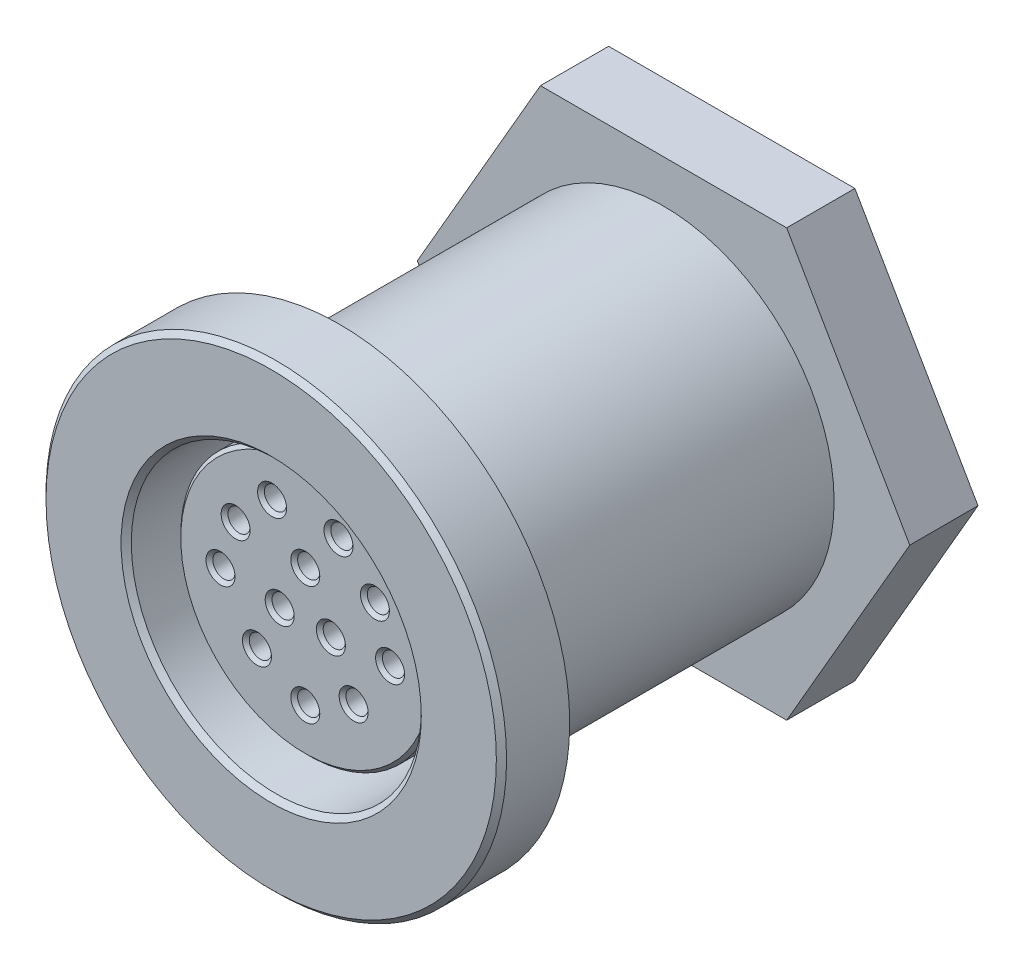
SolidWorks part; units mm, degrees
material "1060 Alloy"
ref_plane "Front Plane" through (0, 0, 0) normal (0, 0, 1) x (1, 0, 0)
ref_plane "Top Plane" through (0, 0, 0) normal (0, 1, 0) x (1, 0, 0)
ref_plane "Right Plane" through (0, 0, 0) normal (1, 0, 0) x (0, 0, -1)
sketch "Sketch1" plane through (0, 0, 0) normal (0, 0, 1) x (1, 0, 0)
  circle A0 centre (0, 0) radius 13.5
extrude "Extrude1" add sketch "Sketch1" along normal blind 4
sketch "Sketch3" plane through (0, 0, 0) normal (0, 0, -1) x (-1, 0, 0)
  circle A0 centre (0, 0) radius 10
extrude "Extrude3" add sketch "Sketch3" along normal blind 25
sketch "Sketch7" plane through (0, 0, 4) normal (0, 0, 1) x (1, 0, 0)
  circle A0 centre (0, 0) radius 8.5
extrude "Cut-Extrude5" cut sketch "Sketch7" against normal blind 16
sketch "Sketch4" plane through (0, 0, -12) normal (0, 0, 1) x (1, 0, 0)
  circle A0 centre (0, 0) radius 7.5
extrude "Extrude4" add sketch "Sketch4" along normal blind 14
chamfer "Chamfer1" distance 0.2 angle 45 1 edges at (7.5, 0, 2)
chamfer "Chamfer3" distance 0.3 angle 45 2 edges at (13.5, 0, 4) (8.5, 0, 4)
sketch "Sketch5" plane through (0, 0, 0) normal (0, 0, -1) x (-1, 0, 0)
  circle A0 centre (0, 0) radius 12
  circle A1 centre (0, 0) radius 10
extrude "Cut-Extrude1" cut sketch "Sketch5" against normal blind 1.5
sketch "Sketch8" plane through (0, 0, -25) normal (0, 0, -1) x (-1, 0, 0)
  circle A0 centre (0, 0) radius 8
extrude "Cut-Extrude6" cut sketch "Sketch8" against normal blind 2
chamfer "Chamfer5" distance 1 angle 45 1 edges at (-10, 0, -25)
sketch "Sketch6" plane through (0, 0, 2) normal (0, 0, 1) x (1, 0, 0)
  line L0 (0, 0) -> (0, 7.3) construction
  line L2 (7.1244, 1.5917) -> (6.262, 3.7519) construction
  circle A0 centre (1.5003, -0.6553) radius 0.65
  circle A1 centre (0, 2.1269) radius 0.65
  circle A2 centre (0, -4.8486) radius 0.65
  circle A3 centre (2.8341, -3.3769) radius 0.65
  circle A4 centre (1.9471, 4.6066) radius 0.65
  circle A5 centre (4.9711, -0.373) radius 0.65
  circle A6 centre (-4.0841, 2.4091) radius 0.65
  circle A7 centre (0, 0) radius 7.3 construction
  circle A8 centre (-4.9711, -0.373) radius 0.65
  circle A9 centre (-1.9471, 4.6066) radius 0.65
  circle A10 centre (-2.8341, -3.3769) radius 0.65
  circle A11 centre (-1.5003, -0.6553) radius 0.65
  circle A12 centre (4.0841, 2.4091) radius 0.65
extrude "Cut-Extrude2" cut sketch "Sketch6" against normal blind 5 contours A2 | A5 | A4 | A3 | A1
chamfer "Chamfer6" distance 0.2 angle 45 12 edges at (-4.7341, 2.4091, 2) (-5.6211, -0.373, 2) (-2.1503, -0.6553, 2) (-3.4841, -3.3769, 2) (0.65, -4.8486, 2) (3.4841, -3.3769, 2) (2.1503, -0.6553, 2) (5.6211, -0.373, 2) (4.7341, 2.4091, 2) (0.65, 2.1269, 2) (2.5971, 4.6066, 2) (-2.5971, 4.6066, 2)
sketch "Sketch9" plane through (0, 0, -23) normal (0, 0, -1) x (-1, 0, 0)
  line L0 (-7.2169, 12.5) -> (7.2169, 12.5)
  line L1 (7.2169, 12.5) -> (14.4338, 0)
  line L2 (14.4338, 0) -> (7.2169, -12.5)
  line L3 (7.2169, -12.5) -> (-7.2169, -12.5)
  line L4 (-7.2169, -12.5) -> (-14.4338, 0)
  line L5 (-14.4338, 0) -> (-7.2169, 12.5)
  dimension "D1" = 25
  dimension "D3" = 12.5
extrude "Extrude5" add sketch "Sketch9" against normal blind 4
